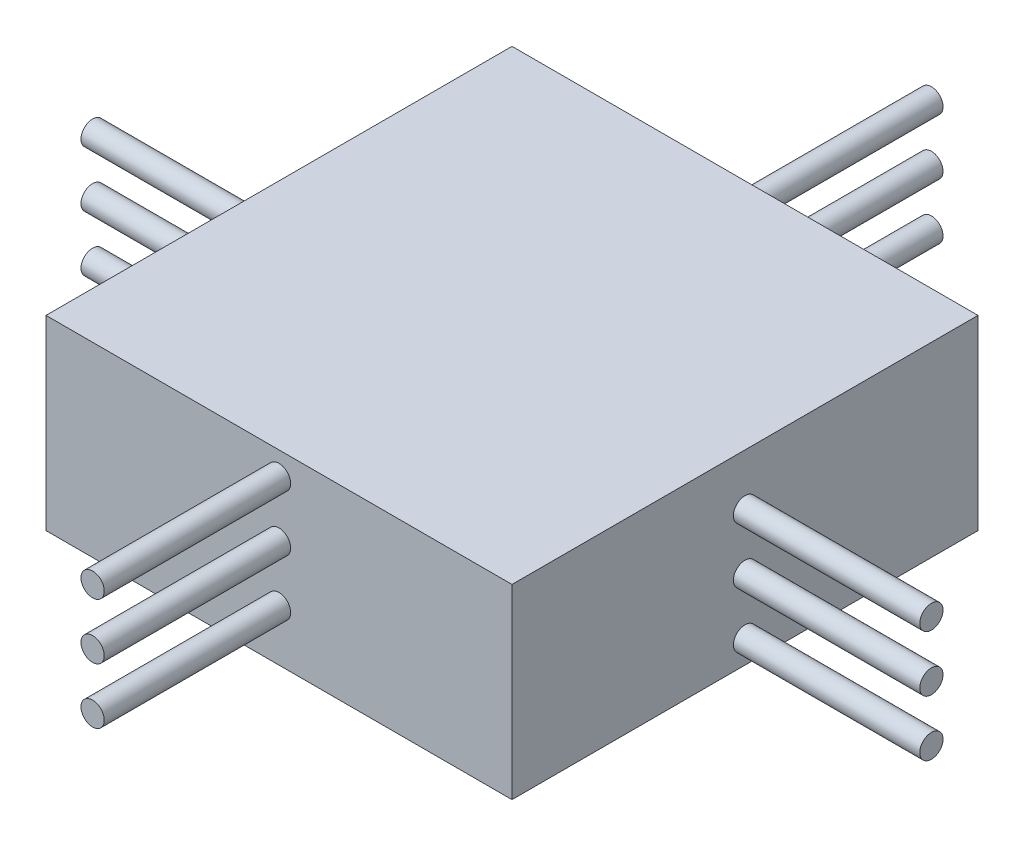
SolidWorks part; units mm, degrees
ref_plane "Front Plane" through (0, 0, 0) normal (0, 0, 1) x (1, 0, 0)
ref_plane "Top Plane" through (0, 0, 0) normal (0, 1, 0) x (1, 0, 0)
ref_plane "Right Plane" through (0, 0, 0) normal (1, 0, 0) x (0, 0, -1)
sketch "Sketch1" plane through (0, 0, 0) normal (0, 1, 0) x (1, 0, 0)
  line L1 (25, -25) -> (-25, -25)
  line L2 (25, -25) -> (25, 25)
  line L3 (25, 25) -> (-25, 25)
  line L4 (-25, -25) -> (-25, 25)
  line L5 (25, -25) -> (-25, 25) construction
  line L6 (25, 25) -> (-25, -25) construction
  point P0 (0, 0)
  dimension "D1" = 50
  dimension "D2" = 50
extrude "Boss-Extrude1" add sketch "Sketch1" along normal blind 20
sketch "Sketch2" plane through (0, 0, 25) normal (0, 0, 1) x (1, 0, 0)
  line L0 (0, 20) -> (0, 0) construction
  line L1 (-25, 20) -> (25, 20) construction
  circle A0 centre (0, 17.5) radius 1.25
  circle A1 centre (0, 11.5) radius 1.25
  circle A2 centre (0, 5.5) radius 1.25
  dimension "D1" = 2.5
  dimension "D2" = 2.5
  dimension "D4" = 6
  dimension "D3" = 3
extrude "Boss-Extrude2" add sketch "Sketch2" along normal blind 20 and the other way blind 70 separate body
sketch "Sketch3" plane through (25, 0, 0) normal (1, 0, 0) x (0, 0, -1)
  line L0 (0, 20) -> (0, 0) construction
  line L1 (-25, 20) -> (25, 20) construction
  circle A0 centre (0, 14.5) radius 1.25
  circle A1 centre (0, 8.5) radius 1.25
  circle A2 centre (0, 2.5) radius 1.25
  dimension "D1" = 2.5
  dimension "D2" = 5.5
  dimension "D4" = 6
  dimension "D3" = 3
extrude "Boss-Extrude3" add sketch "Sketch3" along normal blind 20 and the other way blind 70 separate body
